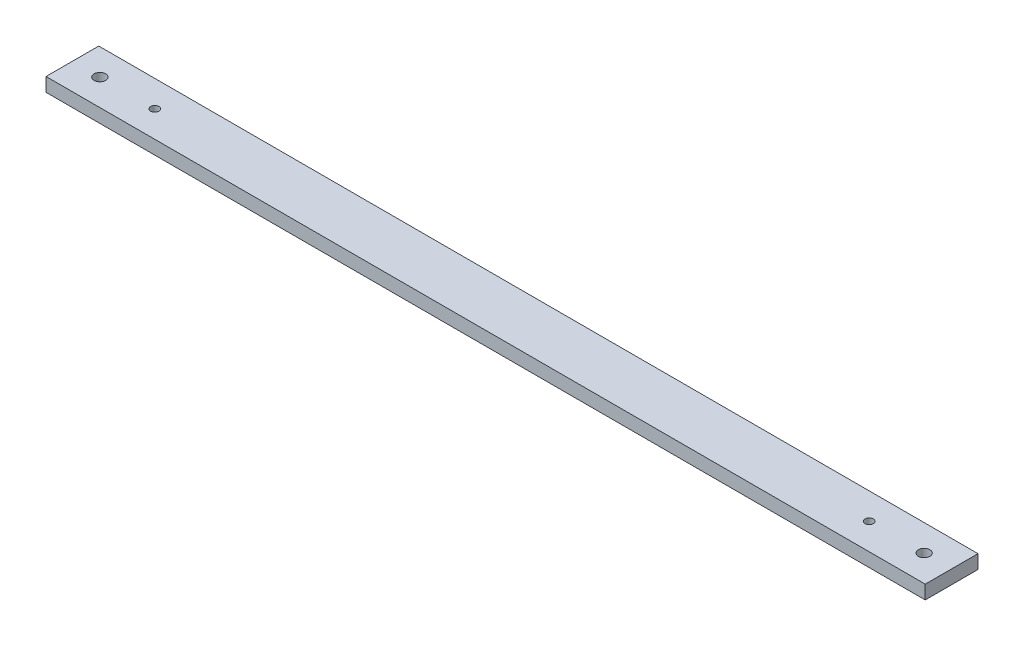
SolidWorks part; units mm, degrees
ref_plane "Front Plane" through (0, 0, 0) normal (0, 0, 1) x (1, 0, 0)
ref_plane "Top Plane" through (0, 0, 0) normal (0, 1, 0) x (1, 0, 0)
ref_plane "Right Plane" through (0, 0, 0) normal (1, 0, 0) x (0, 0, -1)
sketch "Sketch1" plane through (0, 0, 0) normal (0, 1, 0) x (1, 0, 0)
  line L0 (0, 0) -> (130, 0) construction
  line L1 (160, 9.6) -> (-160, 9.6)
  line L2 (160, 9.6) -> (160, -9.6)
  line L3 (160, -9.6) -> (-160, -9.6)
  line L4 (-160, 9.6) -> (-160, -9.6)
  line L5 (160, 9.6) -> (-160, -9.6) construction
  line L6 (160, -9.6) -> (-160, 9.6) construction
  line L7 (0, -55) -> (0, 55) construction
  line L8 (160, 0) -> (150, 0) construction
  circle A0 centre (130, 0) radius 1.5
  circle A1 centre (-130, 0) radius 1.5
  circle A2 centre (150, 0) radius 2.1
  circle A3 centre (-150, 0) radius 2.1
  point P0 (0, 0)
  dimension "D4" = 3
  dimension "D6" = 4.2
  dimension "D1" = 19.2
  dimension "D2" = 320
  dimension "D3" = 130
  dimension "D5" = 10
extrude "Boss-Extrude1" add sketch "Sketch1" along normal blind 5
